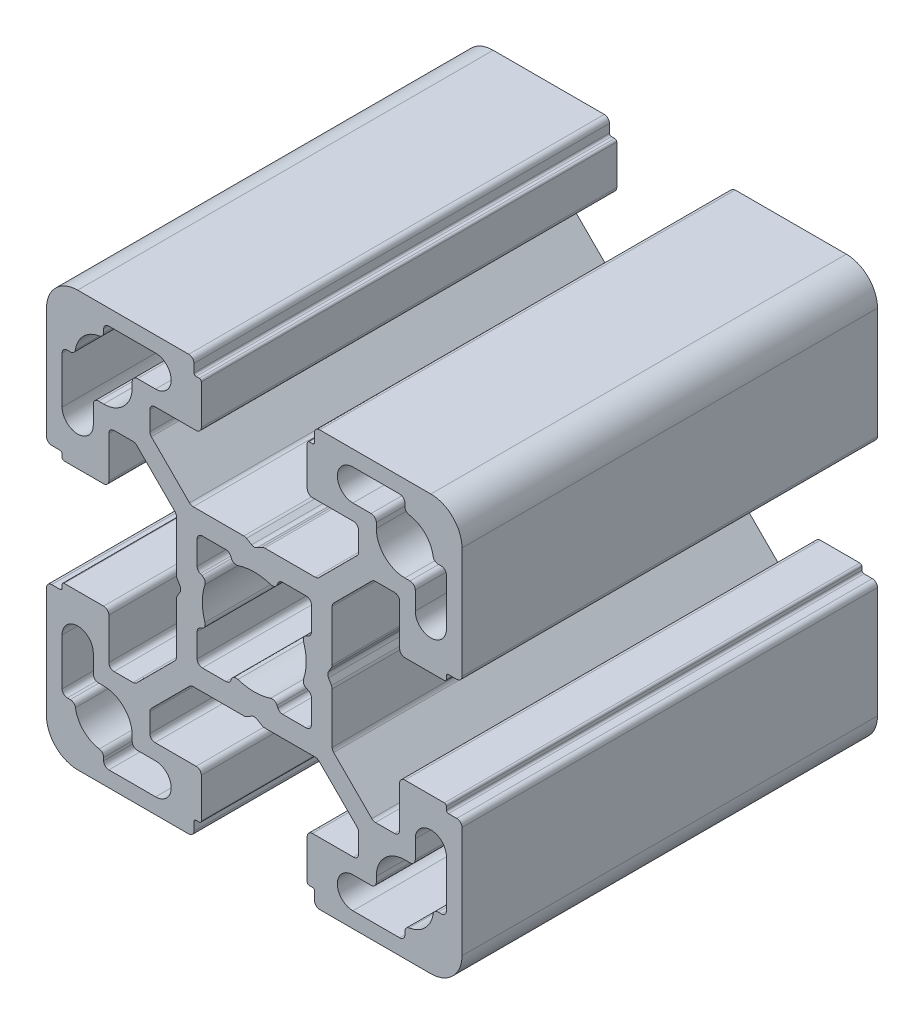
SolidWorks part; units mm, degrees
material "АД31Т ГОСТ 4784-97"
ref_plane "Спереди" through (0, 0, 0) normal (0, 0, 1) x (1, 0, 0)
ref_plane "Сверху" through (0, 0, 0) normal (0, 1, 0) x (1, 0, 0)
ref_plane "Справа" through (0, 0, 0) normal (1, 0, 0) x (0, 0, -1)
sketch "Эскиз1" plane through (0, 0, 0) normal (0, 0, 1) x (1, 0, 0)
  line L0 (-14.5, 18) -> (-14.5, 17.7113)
  line L1 (-18.5, -5.6) -> (-18.5, -5.3)
  line L3 (-14, 18.5) -> (-9.5, 18.5)
  line L4 (18.5, 5.6) -> (18.5, 5.3)
  line L5 (0.25, 7.1443) -> (0.75, 7.433)
  line L6 (1, 7.5) -> (5.8787, 7.5)
  line L7 (5.6, 14) -> (5.6255, 13.9844)
  line L8 (-0.25, 7.1443) -> (-0.75, 7.433)
  line L9 (-5.8787, 7.5) -> (-1, 7.5)
  line L10 (-7.5, 5.8787) -> (-7.5, 1)
  line L11 (-5.6, 18.5) -> (-5.3, 18.5)
  line L12 (10.05, 13.5) -> (10.05, 11.6713)
  line L13 (-14, 5.6) -> (-13.9844, 5.6255)
  line L14 (-13.5, 10.05) -> (-11.6713, 10.05)
  line L15 (-5.1994, 2.2693) -> (-5.0205, 2.1915)
  line L16 (-19.5, 5.8) -> (-18.7, 5.8)
  line L17 (-18.3, 5.1) -> (-14.5, 5.1)
  line L18 (-14, 9.55) -> (-14, 5.6)
  line L19 (-7.6464, 6.2322) -> (-11.3178, 9.9036)
  line L20 (-20, 6.3) -> (-20, 17)
  line L21 (5.1994, -2.2693) -> (5.0205, -2.1915)
  line L22 (-14.5, 18) -> (-14.5, 17.7113)
  line L23 (-14, 18.5) -> (-9.5, 18.5)
  line L24 (-9.5, 15.5) -> (-11.25, 15.5)
  line L25 (-11.75, 15) -> (-11.75, 14.5)
  line L26 (-15, 11.75) -> (-14.5, 11.75)
  line L27 (-15.5, 9.5) -> (-15.5, 11.25)
  line L28 (-18.5, 14) -> (-18.5, 9.5)
  line L29 (-18, 14.5) -> (-17.7113, 14.5)
  line L30 (2.7278, -5.5) -> (5, -5.5)
  line L31 (-2.7278, 5.5) -> (-5, 5.5)
  line L32 (-5.5, 2.7278) -> (-5.5, 5)
  line L33 (5.8, 19.5) -> (5.8, 18.7)
  line L34 (5.1, 18.3) -> (5.1, 14.5)
  line L35 (-2.2693, 5.1994) -> (-2.1915, 5.0205)
  line L36 (9.55, 14) -> (5.6, 14)
  line L37 (-9.5, 15.5) -> (-11.25, 15.5)
  line L38 (2.2693, 5.1994) -> (2.1915, 5.0205)
  line L39 (5.5, 2.7278) -> (5.5, 5)
  line L40 (2.7278, 5.5) -> (5, 5.5)
  line L41 (5.1994, 2.2693) -> (5.0205, 2.1915)
  line L42 (5.5, -2.7278) -> (5.5, -5)
  line L43 (2.2693, -5.1994) -> (2.1915, -5.0205)
  line L44 (-2.2693, -5.1994) -> (-2.1915, -5.0205)
  line L45 (-5.5, -2.7278) -> (-5.5, -5)
  line L46 (-2.7278, -5.5) -> (-5, -5.5)
  line L47 (-5.1994, -2.2693) -> (-5.0205, -2.1915)
  line L48 (-7.1443, 0.25) -> (-7.433, 0.75)
  line L49 (-7.5, -1) -> (-7.5, -5.8787)
  line L50 (-7.1443, -0.25) -> (-7.433, -0.75)
  line L51 (-11.75, 15) -> (-11.75, 14.5)
  line L52 (-15, 11.75) -> (-14.5, 11.75)
  line L53 (-15.5, 9.5) -> (-15.5, 11.25)
  line L54 (-6.3, 20) -> (-17, 20)
  line L55 (-6.2322, 7.6464) -> (-9.9036, 11.3178)
  line L56 (-9.55, 14) -> (-5.6, 14)
  line L57 (-5.1, 18.3) -> (-5.1, 14.5)
  line L58 (-5.8, 19.5) -> (-5.8, 18.7)
  line L59 (-10.05, 13.5) -> (-10.05, 11.6713)
  line L60 (-5.6, 14) -> (-5.6255, 13.9844)
  line L61 (6.2322, 7.6464) -> (9.9036, 11.3178)
  line L62 (6.2322, 7.6464) -> (9.9036, 11.3178)
  line L63 (6.3, 20) -> (17, 20)
  line L64 (15.5, 9.5) -> (15.5, 11.25)
  line L65 (15, 11.75) -> (14.5, 11.75)
  line L66 (11.75, 15) -> (11.75, 14.5)
  line L67 (7.1443, -0.25) -> (7.433, -0.75)
  line L68 (7.5, -1) -> (7.5, -5.8787)
  line L69 (7.1443, 0.25) -> (7.433, 0.75)
  line L70 (5.1994, -2.2693) -> (5.0205, -2.1915)
  line L71 (2.7278, -5.5) -> (5, -5.5)
  line L72 (5.5, -2.7278) -> (5.5, -5)
  line L73 (2.2693, -5.1994) -> (2.1915, -5.0205)
  line L74 (9.5, 15.5) -> (11.25, 15.5)
  line L75 (2.2693, 5.1994) -> (2.1915, 5.0205)
  line L76 (5.5, 2.7278) -> (5.5, 5)
  line L77 (2.7278, 5.5) -> (5, 5.5)
  line L78 (18, 14.5) -> (17.7113, 14.5)
  line L79 (18.5, 14) -> (18.5, 9.5)
  line L80 (15.5, 9.5) -> (15.5, 11.25)
  line L81 (15, 11.75) -> (14.5, 11.75)
  line L82 (11.75, 15) -> (11.75, 14.5)
  line L83 (9.5, 15.5) -> (11.25, 15.5)
  line L84 (14, 18.5) -> (9.5, 18.5)
  line L85 (14.5, 18) -> (14.5, 17.7113)
  line L86 (20, 6.3) -> (20, 17)
  line L87 (7.6464, 6.2322) -> (11.3178, 9.9036)
  line L88 (7.6464, 6.2322) -> (11.3178, 9.9036)
  line L89 (14, 9.55) -> (14, 5.6)
  line L90 (18.3, 5.1) -> (14.5, 5.1)
  line L91 (5.1994, 2.2693) -> (5.0205, 2.1915)
  line L92 (19.5, 5.8) -> (18.7, 5.8)
  line L93 (13.5, 10.05) -> (11.6713, 10.05)
  line L94 (7.5, 5.8787) -> (7.5, 1)
  line L95 (14, 5.6) -> (13.9844, 5.6255)
  line L96 (5.6, 18.5) -> (5.3, 18.5)
  line L97 (5.1994, -2.2693) -> (5.0205, -2.1915)
  line L98 (14, 18.5) -> (9.5, 18.5)
  line L99 (14.5, 18) -> (14.5, 17.7113)
  line L100 (14.5, -18) -> (14.5, -17.7113)
  line L101 (7.6464, -6.2322) -> (11.3178, -9.9036)
  line L102 (14, -18.5) -> (9.5, -18.5)
  line L103 (5.6, -18.5) -> (5.3, -18.5)
  line L104 (14, -5.6) -> (13.9844, -5.6255)
  line L105 (13.5, -10.05) -> (11.6713, -10.05)
  line L106 (19.5, -5.8) -> (18.7, -5.8)
  line L107 (5.1994, -2.2693) -> (5.0205, -2.1915)
  line L108 (18.3, -5.1) -> (14.5, -5.1)
  line L109 (14, -9.55) -> (14, -5.6)
  line L110 (7.6464, -6.2322) -> (11.3178, -9.9036)
  line L111 (2.7278, -5.5) -> (5, -5.5)
  line L112 (5.5, -2.7278) -> (5.5, -5)
  line L113 (2.2693, -5.1994) -> (2.1915, -5.0205)
  line L114 (7.6464, -6.2322) -> (11.3178, -9.9036)
  line L115 (20, -6.3) -> (20, -17)
  line L116 (14.5, -18) -> (14.5, -17.7113)
  line L117 (14, -18.5) -> (9.5, -18.5)
  line L118 (9.5, -15.5) -> (11.25, -15.5)
  line L119 (6.2322, -7.6464) -> (9.9036, -11.3178)
  line L120 (11.75, -15) -> (11.75, -14.5)
  line L121 (15, -11.75) -> (14.5, -11.75)
  line L122 (15.5, -9.5) -> (15.5, -11.25)
  line L123 (18.5, -14) -> (18.5, -9.5)
  line L124 (18, -14.5) -> (17.7113, -14.5)
  line L125 (2.7278, -5.5) -> (5, -5.5)
  line L126 (-6.2322, -7.6464) -> (-9.9036, -11.3178)
  line L127 (5.5, -2.7278) -> (5.5, -5)
  line L128 (2.2693, -5.1994) -> (2.1915, -5.0205)
  line L129 (9.5, -15.5) -> (11.25, -15.5)
  line L130 (11.75, -15) -> (11.75, -14.5)
  line L131 (5.1994, -2.2693) -> (5.0205, -2.1915)
  line L132 (2.7278, -5.5) -> (5, -5.5)
  line L133 (5.5, -2.7278) -> (5.5, -5)
  line L134 (2.2693, -5.1994) -> (2.1915, -5.0205)
  line L135 (15, -11.75) -> (14.5, -11.75)
  line L136 (-2.2693, -5.1994) -> (-2.1915, -5.0205)
  line L137 (15.5, -9.5) -> (15.5, -11.25)
  line L138 (6.3, -20) -> (17, -20)
  line L139 (-5.5, -2.7278) -> (-5.5, -5)
  line L140 (-2.7278, -5.5) -> (-5, -5.5)
  line L141 (6.2322, -7.6464) -> (9.9036, -11.3178)
  line L142 (6.2322, -7.6464) -> (9.9036, -11.3178)
  line L143 (-5.6, -14) -> (-5.6255, -13.9844)
  line L144 (-10.05, -13.5) -> (-10.05, -11.6713)
  line L145 (-5.8, -19.5) -> (-5.8, -18.7)
  line L146 (-5.1, -18.3) -> (-5.1, -14.5)
  line L147 (-9.55, -14) -> (-5.6, -14)
  line L148 (-6.2322, -7.6464) -> (-9.9036, -11.3178)
  line L149 (-6.3, -20) -> (-17, -20)
  line L150 (-7.6464, -6.2322) -> (-11.3178, -9.9036)
  line L151 (-15.5, -9.5) -> (-15.5, -11.25)
  line L152 (-15, -11.75) -> (-14.5, -11.75)
  line L153 (-11.75, -15) -> (-11.75, -14.5)
  line L154 (-5.1994, -2.2693) -> (-5.0205, -2.1915)
  line L155 (-13.5, -10.05) -> (-11.6713, -10.05)
  line L156 (5.1994, -2.2693) -> (5.0205, -2.1915)
  line L157 (2.7278, -5.5) -> (5, -5.5)
  line L158 (-5.8787, -7.5) -> (-1, -7.5)
  line L159 (-0.25, -7.1443) -> (-0.75, -7.433)
  line L160 (5.5, -2.7278) -> (5.5, -5)
  line L161 (1, -7.5) -> (5.8787, -7.5)
  line L162 (0.25, -7.1443) -> (0.75, -7.433)
  line L163 (2.2693, -5.1994) -> (2.1915, -5.0205)
  line L164 (-9.5, -15.5) -> (-11.25, -15.5)
  line L165 (9.55, -14) -> (5.6, -14)
  line L166 (-18.5, 5.6) -> (-18.5, 5.3)
  line L167 (-2.2693, -5.1994) -> (-2.1915, -5.0205)
  line L168 (5.1, -18.3) -> (5.1, -14.5)
  line L169 (5.8, -19.5) -> (5.8, -18.7)
  line L170 (-5.5, -2.7278) -> (-5.5, -5)
  line L171 (-2.7278, -5.5) -> (-5, -5.5)
  line L172 (-18, -14.5) -> (-17.7113, -14.5)
  line L173 (-18.5, -14) -> (-18.5, -9.5)
  line L174 (-15.5, -9.5) -> (-15.5, -11.25)
  line L175 (-15, -11.75) -> (-14.5, -11.75)
  line L176 (-11.75, -15) -> (-11.75, -14.5)
  line L177 (-9.5, -15.5) -> (-11.25, -15.5)
  line L178 (-14, -18.5) -> (-9.5, -18.5)
  line L179 (-14.5, -18) -> (-14.5, -17.7113)
  line L180 (-20, -6.3) -> (-20, -17)
  line L181 (-7.6464, -6.2322) -> (-11.3178, -9.9036)
  line L182 (-14, -9.55) -> (-14, -5.6)
  line L183 (-18.3, -5.1) -> (-14.5, -5.1)
  line L184 (-19.5, -5.8) -> (-18.7, -5.8)
  line L185 (-5.1994, -2.2693) -> (-5.0205, -2.1915)
  line L186 (-13.5, -10.05) -> (-11.6713, -10.05)
  line L187 (-14, -5.6) -> (-13.9844, -5.6255)
  line L188 (10.05, -13.5) -> (10.05, -11.6713)
  line L189 (-5.6, -18.5) -> (-5.3, -18.5)
  line L190 (-5.8787, -7.5) -> (-1, -7.5)
  line L191 (-0.25, -7.1443) -> (-0.75, -7.433)
  line L192 (5.6, -14) -> (5.6255, -13.9844)
  line L193 (1, -7.5) -> (5.8787, -7.5)
  line L194 (0.25, -7.1443) -> (0.75, -7.433)
  line L195 (18.5, -5.6) -> (18.5, -5.3)
  line L196 (-14, -18.5) -> (-9.5, -18.5)
  line L197 (-14.5, -18) -> (-14.5, -17.7113)
  arc A0 (-17, 20) -> (-20, 17) centre (-17, 17) ccw
  arc A1 (-4.7453, 1.5754) -> (-4.7453, -1.5754) centre (0, 0) ccw
  arc A2 (-9.5, 15.5) -> (-9.5, 18.5) centre (-9.5, 17) ccw
  arc A3 (-14.9231, 17.2173) -> (-17.2173, 14.9231) centre (-14.5, 14.5) ccw
  arc A4 (-14.5, 11.75) -> (-11.75, 14.5) centre (-14.5, 14.5) ccw
  arc A5 (-15.5, 9.5) -> (-18.5, 9.5) centre (-17, 9.5) cw
  arc A6 (-11.3178, 9.9036) -> (-11.6713, 10.05) centre (-11.6713, 9.55) ccw
  arc A7 (-13.5, 10.05) -> (-14, 9.55) centre (-13.5, 9.55) ccw
  arc A8 (-14.5, 5.1) -> (-14, 5.6) centre (-14.5, 5.6) ccw
  arc A9 (-20, 6.3) -> (-19.5, 5.8) centre (-19.5, 6.3) ccw
  arc A10 (-11.25, 15.5) -> (-11.75, 15) centre (-11.25, 15) ccw
  arc A11 (-18.3, 5.1) -> (-18.5, 5.3) centre (-18.3, 5.3) cw
  arc A12 (-18.7, 5.8) -> (-18.5, 5.6) centre (-18.7, 5.6) cw
  arc A13 (-7.6464, 6.2322) -> (-7.5, 5.8787) centre (-8, 5.8787) cw
  arc A14 (-15, 11.75) -> (-15.5, 11.25) centre (-15, 11.25) ccw
  arc A15 (-14.5, 18) -> (-14, 18.5) centre (-14, 18) cw
  arc A16 (-18.5, 14) -> (-18, 14.5) centre (-18, 14) cw
  arc A17 (-14.5, 17.7113) -> (-14.9231, 17.2173) centre (-15, 17.7113) cw
  arc A18 (-17.7113, 14.5) -> (-17.2173, 14.9231) centre (-17.7113, 15) ccw
  arc A19 (-5.0205, 2.1915) -> (-4.7453, 1.5754) centre (-5.2198, 1.733) cw
  arc A20 (-2.1915, 5.0205) -> (-1.5754, 4.7453) centre (-1.733, 5.2198) ccw
  arc A21 (-2.2693, 5.1994) -> (-2.7278, 5.5) centre (-2.7278, 5) ccw
  arc A22 (-5, 5.5) -> (-5.5, 5) centre (-5, 5) ccw
  arc A23 (-5.1994, 2.2693) -> (-5.5, 2.7278) centre (-5, 2.7278) cw
  arc A24 (5.1994, 2.2693) -> (5.5, 2.7278) centre (5, 2.7278) ccw
  arc A25 (5, 5.5) -> (5.5, 5) centre (5, 5) cw
  arc A26 (2.2693, 5.1994) -> (2.7278, 5.5) centre (2.7278, 5) cw
  arc A27 (2.1915, 5.0205) -> (1.5754, 4.7453) centre (1.733, 5.2198) cw
  arc A28 (5.0205, 2.1915) -> (4.7453, 1.5754) centre (5.2198, 1.733) ccw
  arc A29 (5.0205, -2.1915) -> (4.7453, -1.5754) centre (5.2198, -1.733) cw
  arc A30 (2.1915, -5.0205) -> (1.5754, -4.7453) centre (1.733, -5.2198) ccw
  arc A31 (2.2693, -5.1994) -> (2.7278, -5.5) centre (2.7278, -5) ccw
  arc A32 (5, -5.5) -> (5.5, -5) centre (5, -5) ccw
  arc A33 (5.1994, -2.2693) -> (5.5, -2.7278) centre (5, -2.7278) cw
  arc A34 (-5.1994, -2.2693) -> (-5.5, -2.7278) centre (-5, -2.7278) ccw
  arc A35 (-5, -5.5) -> (-5.5, -5) centre (-5, -5) cw
  arc A36 (-2.2693, -5.1994) -> (-2.7278, -5.5) centre (-2.7278, -5) cw
  arc A37 (-2.1915, -5.0205) -> (-1.5754, -4.7453) centre (-1.733, -5.2198) cw
  arc A38 (-5.0205, -2.1915) -> (-4.7453, -1.5754) centre (-5.2198, -1.733) ccw
  arc A39 (1.5754, 4.7453) -> (-1.5754, 4.7453) centre (0, 0) ccw
  arc A40 (4.7453, -1.5754) -> (4.7453, 1.5754) centre (0, 0) ccw
  arc A41 (-1.5754, -4.7453) -> (1.5754, -4.7453) centre (0, 0) ccw
  arc A42 (-7.433, -0.75) -> (-7.5, -1) centre (-7, -1) ccw
  arc A43 (-7.1443, -0.25) -> (-7.1443, 0.25) centre (-7.5774, 0) ccw
  arc A44 (-7.433, 0.75) -> (-7.5, 1) centre (-7, 1) cw
  arc A45 (-14.5, 17.7113) -> (-14.9231, 17.2173) centre (-15, 17.7113) cw
  arc A46 (-17.7113, 14.5) -> (-17.2173, 14.9231) centre (-17.7113, 15) ccw
  arc A47 (-14, 18.5) -> (-14.5, 18) centre (-14, 18) ccw
  arc A48 (-11.75, 15) -> (-11.25, 15.5) centre (-11.25, 15) cw
  arc A49 (-6.2322, 7.6464) -> (-5.8787, 7.5) centre (-5.8787, 8) ccw
  arc A50 (-5.8, 18.7) -> (-5.6, 18.5) centre (-5.6, 18.7) ccw
  arc A51 (-5.1, 18.3) -> (-5.3, 18.5) centre (-5.3, 18.3) ccw
  arc A52 (-15.5, 11.25) -> (-15, 11.75) centre (-15, 11.25) cw
  arc A53 (-6.3, 20) -> (-5.8, 19.5) centre (-6.3, 19.5) cw
  arc A54 (-5.1, 14.5) -> (-5.6, 14) centre (-5.6, 14.5) cw
  arc A55 (-10.05, 13.5) -> (-9.55, 14) centre (-9.55, 13.5) cw
  arc A56 (-9.9036, 11.3178) -> (-10.05, 11.6713) centre (-9.55, 11.6713) cw
  arc A57 (-9.5, 15.5) -> (-9.5, 18.5) centre (-9.5, 17) ccw
  arc A58 (-15.5, 9.5) -> (-18.5, 9.5) centre (-17, 9.5) cw
  arc A59 (-0.75, 7.433) -> (-1, 7.5) centre (-1, 7) ccw
  arc A60 (0.25, 7.1443) -> (-0.25, 7.1443) centre (0, 7.5774) cw
  arc A61 (0.75, 7.433) -> (1, 7.5) centre (1, 7) cw
  arc A62 (15.5, 9.5) -> (18.5, 9.5) centre (17, 9.5) ccw
  arc A63 (9.5, 15.5) -> (9.5, 18.5) centre (9.5, 17) cw
  arc A64 (9.9036, 11.3178) -> (10.05, 11.6713) centre (9.55, 11.6713) ccw
  arc A65 (9.9036, 11.3178) -> (10.05, 11.6713) centre (9.55, 11.6713) ccw
  arc A66 (10.05, 13.5) -> (9.55, 14) centre (9.55, 13.5) ccw
  arc A67 (5.1, 14.5) -> (5.6, 14) centre (5.6, 14.5) ccw
  arc A68 (6.3, 20) -> (5.8, 19.5) centre (6.3, 19.5) ccw
  arc A69 (15.5, 11.25) -> (15, 11.75) centre (15, 11.25) ccw
  arc A70 (5.1, 18.3) -> (5.3, 18.5) centre (5.3, 18.3) cw
  arc A71 (6.2322, 7.6464) -> (5.8787, 7.5) centre (5.8787, 8) cw
  arc A72 (5.8, 18.7) -> (5.6, 18.5) centre (5.6, 18.7) cw
  arc A73 (6.2322, 7.6464) -> (5.8787, 7.5) centre (5.8787, 8) cw
  arc A74 (11.75, 15) -> (11.25, 15.5) centre (11.25, 15) ccw
  arc A75 (14, 18.5) -> (14.5, 18) centre (14, 18) cw
  arc A76 (7.433, 0.75) -> (7.5, 1) centre (7, 1) ccw
  arc A77 (7.1443, -0.25) -> (7.1443, 0.25) centre (7.5774, 0) cw
  arc A78 (7.433, -0.75) -> (7.5, -1) centre (7, -1) cw
  arc A79 (5.0205, -2.1915) -> (4.7453, -1.5754) centre (5.2198, -1.733) cw
  arc A80 (2.2693, -5.1994) -> (2.7278, -5.5) centre (2.7278, -5) ccw
  arc A81 (5, -5.5) -> (5.5, -5) centre (5, -5) ccw
  arc A82 (5.1994, -2.2693) -> (5.5, -2.7278) centre (5, -2.7278) cw
  arc A83 (5.1994, 2.2693) -> (5.5, 2.7278) centre (5, 2.7278) ccw
  arc A84 (5, 5.5) -> (5.5, 5) centre (5, 5) cw
  arc A85 (2.2693, 5.1994) -> (2.7278, 5.5) centre (2.7278, 5) cw
  arc A86 (5.0205, 2.1915) -> (4.7453, 1.5754) centre (5.2198, 1.733) ccw
  arc A87 (17.7113, 14.5) -> (17.2173, 14.9231) centre (17.7113, 15) cw
  arc A88 (14.5, 17.7113) -> (14.9231, 17.2173) centre (15, 17.7113) ccw
  arc A89 (5, 5.5) -> (5.5, 5) centre (5, 5) cw
  arc A90 (17.7113, 14.5) -> (17.2173, 14.9231) centre (17.7113, 15) cw
  arc A91 (14.5, 17.7113) -> (14.9231, 17.2173) centre (15, 17.7113) ccw
  arc A92 (7.6464, 6.2322) -> (7.5, 5.8787) centre (8, 5.8787) ccw
  arc A93 (18.5, 14) -> (18, 14.5) centre (18, 14) ccw
  arc A94 (14.5, 18) -> (14, 18.5) centre (14, 18) ccw
  arc A95 (15, 11.75) -> (15.5, 11.25) centre (15, 11.25) cw
  arc A96 (7.6464, 6.2322) -> (7.5, 5.8787) centre (8, 5.8787) ccw
  arc A97 (18.7, 5.8) -> (18.5, 5.6) centre (18.7, 5.6) ccw
  arc A98 (18.3, 5.1) -> (18.5, 5.3) centre (18.3, 5.3) ccw
  arc A99 (11.3178, 9.9036) -> (11.6713, 10.05) centre (11.6713, 9.55) cw
  arc A100 (11.25, 15.5) -> (11.75, 15) centre (11.25, 15) cw
  arc A101 (20, 6.3) -> (19.5, 5.8) centre (19.5, 6.3) cw
  arc A102 (14.5, 5.1) -> (14, 5.6) centre (14.5, 5.6) cw
  arc A103 (13.5, 10.05) -> (14, 9.55) centre (13.5, 9.55) cw
  arc A104 (4.7453, 1.5754) -> (4.7453, -1.5754) centre (0, 0) cw
  arc A105 (11.3178, 9.9036) -> (11.6713, 10.05) centre (11.6713, 9.55) cw
  arc A106 (15.5, 9.5) -> (18.5, 9.5) centre (17, 9.5) ccw
  arc A107 (14.5, 11.75) -> (11.75, 14.5) centre (14.5, 14.5) cw
  arc A108 (14.9231, 17.2173) -> (17.2173, 14.9231) centre (14.5, 14.5) cw
  arc A109 (9.5, 15.5) -> (9.5, 18.5) centre (9.5, 17) cw
  arc A110 (17, 20) -> (20, 17) centre (17, 17) cw
  arc A111 (11.3178, -9.9036) -> (11.6713, -10.05) centre (11.6713, -9.55) ccw
  arc A112 (17, -20) -> (20, -17) centre (17, -17) ccw
  arc A113 (9.5, -15.5) -> (9.5, -18.5) centre (9.5, -17) ccw
  arc A114 (14.9231, -17.2173) -> (17.2173, -14.9231) centre (14.5, -14.5) ccw
  arc A115 (14.5, -11.75) -> (11.75, -14.5) centre (14.5, -14.5) ccw
  arc A116 (15.5, -9.5) -> (18.5, -9.5) centre (17, -9.5) cw
  arc A117 (11.3178, -9.9036) -> (11.6713, -10.05) centre (11.6713, -9.55) ccw
  arc A118 (7.6464, -6.2322) -> (7.5, -5.8787) centre (8, -5.8787) cw
  arc A119 (13.5, -10.05) -> (14, -9.55) centre (13.5, -9.55) ccw
  arc A120 (14.5, -5.1) -> (14, -5.6) centre (14.5, -5.6) ccw
  arc A121 (20, -6.3) -> (19.5, -5.8) centre (19.5, -6.3) ccw
  arc A122 (11.25, -15.5) -> (11.75, -15) centre (11.25, -15) ccw
  arc A123 (11.3178, -9.9036) -> (11.6713, -10.05) centre (11.6713, -9.55) ccw
  arc A124 (5.0205, -2.1915) -> (4.7453, -1.5754) centre (5.2198, -1.733) cw
  arc A125 (2.2693, -5.1994) -> (2.7278, -5.5) centre (2.7278, -5) ccw
  arc A126 (5, -5.5) -> (5.5, -5) centre (5, -5) ccw
  arc A127 (5.1994, -2.2693) -> (5.5, -2.7278) centre (5, -2.7278) cw
  arc A128 (18.3, -5.1) -> (18.5, -5.3) centre (18.3, -5.3) cw
  arc A129 (18.7, -5.8) -> (18.5, -5.6) centre (18.7, -5.6) cw
  arc A130 (7.6464, -6.2322) -> (7.5, -5.8787) centre (8, -5.8787) cw
  arc A131 (15, -11.75) -> (15.5, -11.25) centre (15, -11.25) ccw
  arc A132 (6.2322, -7.6464) -> (5.8787, -7.5) centre (5.8787, -8) ccw
  arc A133 (14.5, -18) -> (14, -18.5) centre (14, -18) cw
  arc A134 (18.5, -14) -> (18, -14.5) centre (18, -14) cw
  arc A135 (7.6464, -6.2322) -> (7.5, -5.8787) centre (8, -5.8787) cw
  arc A136 (14.5, -17.7113) -> (14.9231, -17.2173) centre (15, -17.7113) cw
  arc A137 (17.7113, -14.5) -> (17.2173, -14.9231) centre (17.7113, -15) ccw
  arc A138 (5, -5.5) -> (5.5, -5) centre (5, -5) ccw
  arc A139 (9.9036, -11.3178) -> (10.05, -11.6713) centre (9.55, -11.6713) cw
  arc A140 (14.5, -17.7113) -> (14.9231, -17.2173) centre (15, -17.7113) cw
  arc A141 (17.7113, -14.5) -> (17.2173, -14.9231) centre (17.7113, -15) ccw
  arc A142 (0.75, -7.433) -> (1, -7.5) centre (1, -7) ccw
  arc A143 (0.25, -7.1443) -> (-0.25, -7.1443) centre (0, -7.5774) ccw
  arc A144 (-0.75, -7.433) -> (-1, -7.5) centre (-1, -7) cw
  arc A145 (2.2693, -5.1994) -> (2.7278, -5.5) centre (2.7278, -5) ccw
  arc A146 (5, -5.5) -> (5.5, -5) centre (5, -5) ccw
  arc A147 (-9.9036, -11.3178) -> (-10.05, -11.6713) centre (-9.55, -11.6713) ccw
  arc A148 (5.1994, -2.2693) -> (5.5, -2.7278) centre (5, -2.7278) cw
  arc A149 (14, -18.5) -> (14.5, -18) centre (14, -18) ccw
  arc A150 (11.75, -15) -> (11.25, -15.5) centre (11.25, -15) cw
  arc A151 (6.2322, -7.6464) -> (5.8787, -7.5) centre (5.8787, -8) ccw
  arc A152 (5.8, -18.7) -> (5.6, -18.5) centre (5.6, -18.7) ccw
  arc A153 (6.2322, -7.6464) -> (5.8787, -7.5) centre (5.8787, -8) ccw
  arc A154 (-6.2322, -7.6464) -> (-5.8787, -7.5) centre (-5.8787, -8) cw
  arc A155 (5.1, -18.3) -> (5.3, -18.5) centre (5.3, -18.3) ccw
  arc A156 (15.5, -11.25) -> (15, -11.75) centre (15, -11.25) cw
  arc A157 (6.3, -20) -> (5.8, -19.5) centre (6.3, -19.5) cw
  arc A158 (5.1, -14.5) -> (5.6, -14) centre (5.6, -14.5) cw
  arc A159 (1.5754, -4.7453) -> (-1.5754, -4.7453) centre (0, 0) cw
  arc A160 (5.0205, -2.1915) -> (4.7453, -1.5754) centre (5.2198, -1.733) cw
  arc A161 (2.1915, -5.0205) -> (1.5754, -4.7453) centre (1.733, -5.2198) ccw
  arc A162 (2.2693, -5.1994) -> (2.7278, -5.5) centre (2.7278, -5) ccw
  arc A163 (5, -5.5) -> (5.5, -5) centre (5, -5) ccw
  arc A164 (5.1994, -2.2693) -> (5.5, -2.7278) centre (5, -2.7278) cw
  arc A165 (-5.1994, -2.2693) -> (-5.5, -2.7278) centre (-5, -2.7278) ccw
  arc A166 (-5, -5.5) -> (-5.5, -5) centre (-5, -5) cw
  arc A167 (-2.2693, -5.1994) -> (-2.7278, -5.5) centre (-2.7278, -5) cw
  arc A168 (-2.1915, -5.0205) -> (-1.5754, -4.7453) centre (-1.733, -5.2198) cw
  arc A169 (-5.0205, -2.1915) -> (-4.7453, -1.5754) centre (-5.2198, -1.733) ccw
  arc A170 (10.05, -13.5) -> (9.55, -14) centre (9.55, -13.5) cw
  arc A171 (9.9036, -11.3178) -> (10.05, -11.6713) centre (9.55, -11.6713) cw
  arc A172 (9.9036, -11.3178) -> (10.05, -11.6713) centre (9.55, -11.6713) cw
  arc A173 (9.5, -15.5) -> (9.5, -18.5) centre (9.5, -17) ccw
  arc A174 (15.5, -9.5) -> (18.5, -9.5) centre (17, -9.5) cw
  arc A175 (-7.6464, -6.2322) -> (-7.5, -5.8787) centre (-8, -5.8787) ccw
  arc A176 (0.75, -7.433) -> (1, -7.5) centre (1, -7) ccw
  arc A177 (0.25, -7.1443) -> (-0.25, -7.1443) centre (0, -7.5774) ccw
  arc A178 (-0.75, -7.433) -> (-1, -7.5) centre (-1, -7) cw
  arc A179 (-15.5, -9.5) -> (-18.5, -9.5) centre (-17, -9.5) ccw
  arc A180 (-9.5, -15.5) -> (-9.5, -18.5) centre (-9.5, -17) cw
  arc A181 (-9.9036, -11.3178) -> (-10.05, -11.6713) centre (-9.55, -11.6713) ccw
  arc A182 (-11.3178, -9.9036) -> (-11.6713, -10.05) centre (-11.6713, -9.55) cw
  arc A183 (-10.05, -13.5) -> (-9.55, -14) centre (-9.55, -13.5) ccw
  arc A184 (-5.1, -14.5) -> (-5.6, -14) centre (-5.6, -14.5) ccw
  arc A185 (-6.3, -20) -> (-5.8, -19.5) centre (-6.3, -19.5) ccw
  arc A186 (-15.5, -11.25) -> (-15, -11.75) centre (-15, -11.25) ccw
  arc A187 (-5.1, -18.3) -> (-5.3, -18.5) centre (-5.3, -18.3) cw
  arc A188 (-5.8, -18.7) -> (-5.6, -18.5) centre (-5.6, -18.7) cw
  arc A189 (-6.2322, -7.6464) -> (-5.8787, -7.5) centre (-5.8787, -8) cw
  arc A190 (-11.75, -15) -> (-11.25, -15.5) centre (-11.25, -15) ccw
  arc A191 (-14, -18.5) -> (-14.5, -18) centre (-14, -18) cw
  arc A192 (-17.7113, -14.5) -> (-17.2173, -14.9231) centre (-17.7113, -15) cw
  arc A193 (-14.5, -17.7113) -> (-14.9231, -17.2173) centre (-15, -17.7113) ccw
  arc A194 (1.5754, -4.7453) -> (-1.5754, -4.7453) centre (0, 0) cw
  arc A195 (2.1915, -5.0205) -> (1.5754, -4.7453) centre (1.733, -5.2198) ccw
  arc A196 (2.2693, -5.1994) -> (2.7278, -5.5) centre (2.7278, -5) ccw
  arc A197 (5, -5.5) -> (5.5, -5) centre (5, -5) ccw
  arc A198 (5.1994, -2.2693) -> (5.5, -2.7278) centre (5, -2.7278) cw
  arc A199 (-5.1994, -2.2693) -> (-5.5, -2.7278) centre (-5, -2.7278) ccw
  arc A200 (-5, -5.5) -> (-5.5, -5) centre (-5, -5) cw
  arc A201 (-2.2693, -5.1994) -> (-2.7278, -5.5) centre (-2.7278, -5) cw
  arc A202 (-2.1915, -5.0205) -> (-1.5754, -4.7453) centre (-1.733, -5.2198) cw
  arc A203 (-17.7113, -14.5) -> (-17.2173, -14.9231) centre (-17.7113, -15) cw
  arc A204 (-14.5, -17.7113) -> (-14.9231, -17.2173) centre (-15, -17.7113) ccw
  arc A205 (-18.5, -14) -> (-18, -14.5) centre (-18, -14) ccw
  arc A206 (-14.5, -18) -> (-14, -18.5) centre (-14, -18) ccw
  arc A207 (-15, -11.75) -> (-15.5, -11.25) centre (-15, -11.25) cw
  arc A208 (-7.6464, -6.2322) -> (-7.5, -5.8787) centre (-8, -5.8787) ccw
  arc A209 (-18.7, -5.8) -> (-18.5, -5.6) centre (-18.7, -5.6) ccw
  arc A210 (-18.3, -5.1) -> (-18.5, -5.3) centre (-18.3, -5.3) ccw
  arc A211 (-11.25, -15.5) -> (-11.75, -15) centre (-11.25, -15) cw
  arc A212 (-20, -6.3) -> (-19.5, -5.8) centre (-19.5, -6.3) cw
  arc A213 (-14.5, -5.1) -> (-14, -5.6) centre (-14.5, -5.6) cw
  arc A214 (-13.5, -10.05) -> (-14, -9.55) centre (-13.5, -9.55) cw
  arc A215 (-11.3178, -9.9036) -> (-11.6713, -10.05) centre (-11.6713, -9.55) cw
  arc A216 (-15.5, -9.5) -> (-18.5, -9.5) centre (-17, -9.5) ccw
  arc A217 (-14.5, -11.75) -> (-11.75, -14.5) centre (-14.5, -14.5) cw
  arc A218 (-14.9231, -17.2173) -> (-17.2173, -14.9231) centre (-14.5, -14.5) cw
  arc A219 (-9.5, -15.5) -> (-9.5, -18.5) centre (-9.5, -17) cw
  arc A220 (-17, -20) -> (-20, -17) centre (-17, -17) cw
  point P0 (0, 0)
  point P6 (0, 0)
  point P52 (-11.75, 15.5)
  point P57 (-20, 5.8)
  point P61 (-15.5, 11.75)
  point P64 (-14.5, 18.5)
  point P67 (-18.5, 14.5)
  point P70 (-14.5, 17.25)
  point P73 (-17.25, 14.5)
  point P87 (-2.4, 5.5)
  point P93 (-5.5, 2.4)
  point P111 (5.5, 2.4)
  point P112 (2.4, 5.5)
  point P143 (2.4, -5.5)
  point P144 (5.5, -2.4)
  point P145 (-5.5, -2.4)
  point P146 (-2.4, -5.5)
  point P175 (-5.8, 20)
  point P257 (5.8, 20)
  point P258 (17.25, 14.5)
  point P259 (14.5, 17.25)
  point P260 (18.5, 14.5)
  point P261 (14.5, 18.5)
  point P262 (15.5, 11.75)
  point P263 (20, 5.8)
  point P264 (11.75, 15.5)
  point P421 (11.75, -15.5)
  point P422 (20, -5.8)
  point P423 (15.5, -11.75)
  point P424 (14.5, -18.5)
  point P425 (18.5, -14.5)
  point P426 (14.5, -17.25)
  point P427 (17.25, -14.5)
  point P428 (5.8, -20)
  point P429 (-5.8, -20)
  point P430 (-17.25, -14.5)
  point P431 (-14.5, -17.25)
  point P432 (-18.5, -14.5)
  point P433 (-14.5, -18.5)
  point P434 (-15.5, -11.75)
  point P435 (-20, -5.8)
  point P436 (-11.75, -15.5)
extrude "Бобышка-Вытянуть1" add sketch "Эскиз1" along normal blind 40
